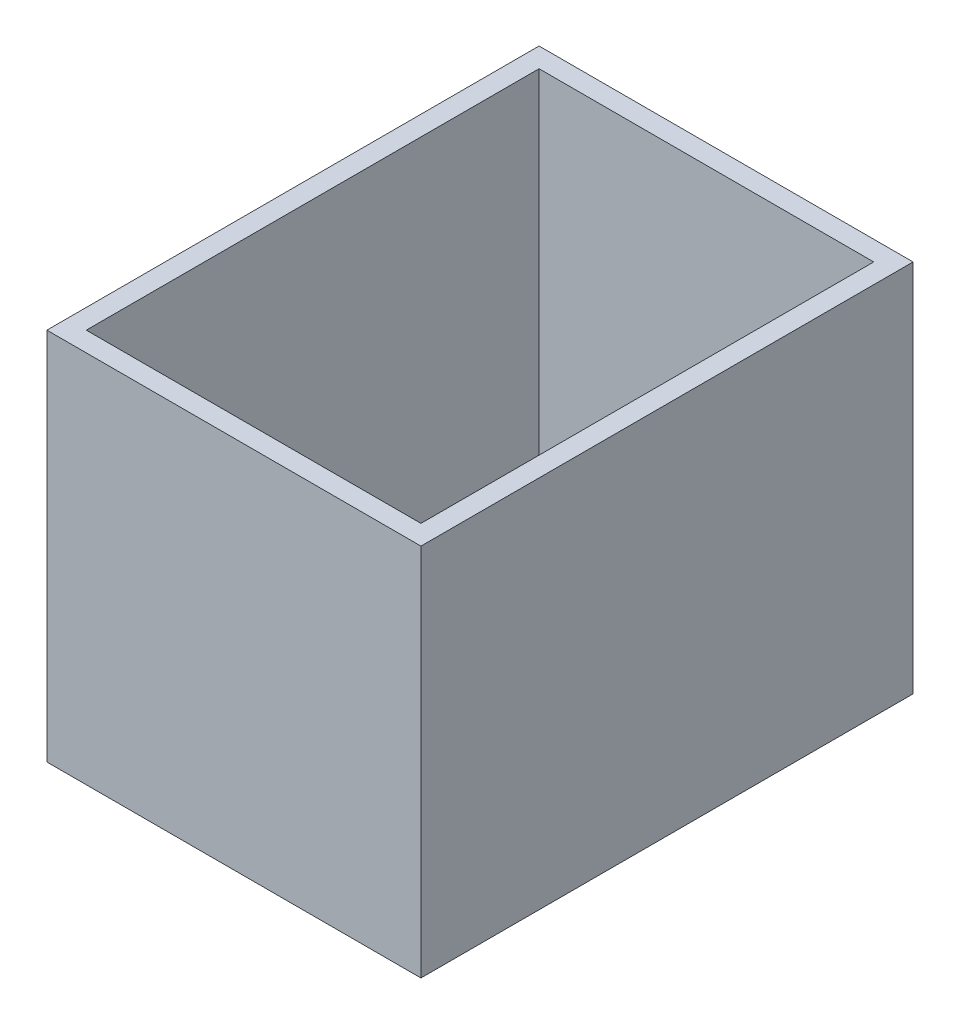
SolidWorks part; units mm, degrees
ref_plane "Front Plane" through (0, 0, 0) normal (0, 0, 1) x (1, 0, 0)
ref_plane "Top Plane" through (0, 0, 0) normal (0, 1, 0) x (1, 0, 0)
ref_plane "Right Plane" through (0, 0, 0) normal (1, 0, 0) x (0, 0, -1)
sketch "Sketch2" plane through (0, 0, 0) normal (0, 0, 1) x (1, 0, 0)
  line L1 (11.8949, 32.2575) -> (108.4149, 32.2575)
  line L2 (11.8949, 32.2575) -> (11.8949, -64.2625)
  line L3 (11.8949, -64.2625) -> (108.4149, -64.2625)
  line L4 (108.4149, 32.2575) -> (108.4149, -64.2625)
extrude "Boss-Extrude1" add sketch "Sketch2" along normal blind 127
sketch "Sketch3" plane through (0, 32.2575, 0) normal (0, 1, 0) x (1, 0, 0)
  line L9 (16.9749, -121.92) -> (103.3349, -121.92)
  line L10 (16.9749, -121.92) -> (16.9749, -5.08)
  line L11 (16.9749, -5.08) -> (103.3349, -5.08)
  line L12 (103.3349, -121.92) -> (103.3349, -5.08)
extrude "Cut-Extrude1" cut sketch "Sketch3" against normal blind 91.44
